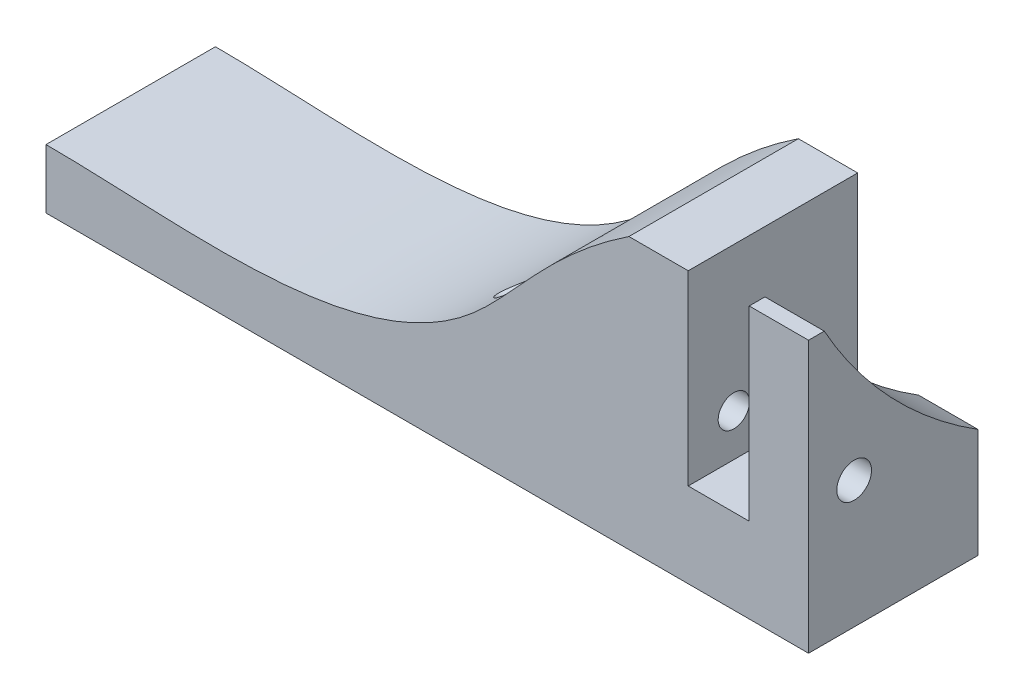
SolidWorks part; units mm, degrees
ref_plane "Front Plane" through (0, 0, 0) normal (0, 0, 1) x (1, 0, 0)
ref_plane "Top Plane" through (0, 0, 0) normal (0, 1, 0) x (1, 0, 0)
ref_plane "Right Plane" through (0, 0, 0) normal (1, 0, 0) x (0, 0, -1)
sketch "Sketch1" plane through (0, 0, 0) normal (0, 0, 1) x (1, 0, 0)
  line L0 (0, 130.3955) -> (0, 108.3955)
  line L1 (0, 108.3955) -> (-7.2, 108.3955)
  line L2 (-7.2, 108.3955) -> (-7.2, 130.3955)
  line L3 (-7.2, 130.3955) -> (-14.2, 130.3955)
  line L5 (-83, 105.3955) -> (-83, 98.3955)
  line L6 (-83, 98.3955) -> (7, 98.3955)
  line L7 (7, 98.3955) -> (7, 130.3955)
  line L8 (7, 130.3955) -> (0, 130.3955)
  line L9 (-83, 105.3955) -> (-49.9151, 105.3955) construction
  line L10 (-96.0454, 105.3955) -> (-69.9517, 105.3955) construction
  spline S0 degree 3 poles (-14.2, 130.3955) (-23.5306, 124.2056) (-38.4462, 100.3183) (-66.6915, 105.3955) (-83, 105.3955) knots 0 0 0 0 0.267224 1 1 1 1
  dimension "D1" = 7.2
  dimension "D2" = 7
  dimension "D3" = 22
  dimension "D4" = 10
  dimension "D5" = 90
  dimension "D6" = 7
extrude "Boss-Extrude1" add sketch "Sketch1" along normal blind 20
sketch "Sketch2" plane through (7, 0, 0) normal (1, 0, 0) x (0, 0, -1)
  line L1 (-14.6158, 113.3955) -> (28.1642, 156.1755) construction
  line L3 (-20, 98.3955) -> (0, 98.3955) construction
  circle A0 centre (28.1642, 156.1755) radius 53
  circle A1 centre (-14.6158, 113.3955) radius 2.05
  circle A2 centre (-14.6158, 113.3955) radius 5 construction
  circle A3 centre (-14.6158, 113.3955) radius 2 construction
  point P7 (-15, 111.6936)
  dimension "D1" = 106
  dimension "D3" = 4.1
  dimension "D4" = 10
  dimension "D2" = 60.5
  dimension "D5" = 45
extrude "Cut-Extrude1" cut sketch "Sketch2" against normal up to surface (14.2 mm away) up to face at (-7.2, 119.3955, 10)
sketch "Sketch4" plane through (7, 0, 0) normal (1, 0, 0) x (0, 0, -1)
  circle A0 centre (-14.6158, 113.3955) radius 1.85
  dimension "D1" = 3.7
extrude "Cut-Extrude2" cut sketch "Sketch4" against normal blind 56
